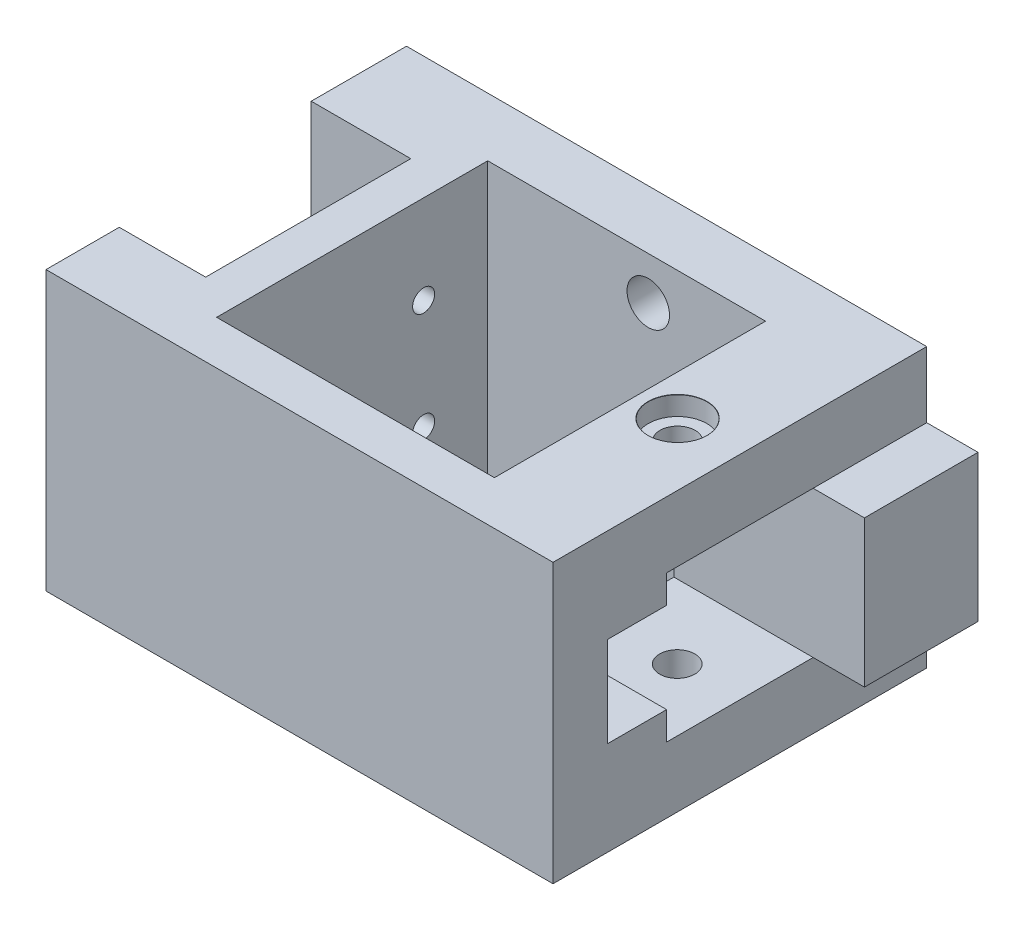
SolidWorks part; units mm, degrees
ref_plane "Alzado" through (0, 0, 0) normal (0, 0, 1) x (1, 0, 0)
ref_plane "Planta" through (0, 0, 0) normal (0, 1, 0) x (1, 0, 0)
ref_plane "Vista lateral" through (0, 0, 0) normal (1, 0, 0) x (0, 0, -1)
sketch "Croquis1" plane through (0, 0, 0) normal (0, 1, 0) x (1, 0, 0)
  line L0 (-121.6471, 30.8824) -> (-62.6471, 30.8824)
  line L1 (-62.6471, 30.8824) -> (-62.6471, -18.1176)
  line L2 (-62.6471, -18.1176) -> (-121.6471, -18.1176)
  line L3 (-121.6471, -7.1176) -> (-108.0588, -7.1176)
  line L4 (-108.0588, -7.1176) -> (-108.0588, 19.8824)
  line L5 (-108.0588, 19.8824) -> (-121.6471, 19.8824)
  line L6 (-121.6471, 19.8824) -> (-121.6471, 30.8824)
  line L7 (-121.6471, -7.1176) -> (-121.6471, -18.1176)
  dimension "D1" = 11
  dimension "D2" = 11
  dimension "D3" = 27
  dimension "D4" = 49
  dimension "D5" = 59
extrude "Saliente-Extruir1" add sketch "Croquis1" along normal blind 38
sketch "Croquis2" plane through (0, 38, 0) normal (0, 1, 0) x (1, 0, 0)
  line L0 (-108.0588, 19.8824) -> (-108.0588, 30.8824) construction
  line L1 (-62.6471, 30.8824) -> (-121.6471, 30.8824) construction
  line L2 (-108.0588, 19.8824) -> (-108.0588, -18.1176) construction
  line L3 (-121.6471, -18.1176) -> (-62.6471, -18.1176) construction
  line L4 (-102.5588, 24.8824) -> (-102.5588, -12.1176)
  line L5 (-102.5588, -12.1176) -> (-69.6471, -12.1176)
  line L6 (-69.6471, -12.1176) -> (-69.6471, 24.8824)
  line L7 (-69.6471, 24.8824) -> (-102.5588, 24.8824)
  line L8 (-62.6471, -18.1176) -> (-62.6471, 30.8824) construction
  dimension "D1" = 7
  dimension "D2" = 11
  dimension "D3" = 6
  dimension "D4" = 6
extrude "Cortar-Extruir1" cut sketch "Croquis2" against normal blind 38
sketch "Croquis3" plane through (-102.5588, 0, 0) normal (1, 0, 0) x (0, 0, -1)
  line L0 (19.4824, 32.1) -> (-6.7176, 32.1) construction
  line L1 (-6.7176, 32.1) -> (-6.7176, 5.9) construction
  line L2 (-6.7176, 5.9) -> (19.4824, 5.9) construction
  line L3 (19.4824, 5.9) -> (19.4824, 32.1) construction
  line L4 (-7.1176, 38) -> (-7.1176, 0) construction
  line L5 (19.8824, 0) -> (-7.1176, 0) construction
  circle A0 centre (16.1324, 10.875) radius 1.5
  circle A1 centre (16.1324, 25.875) radius 1.5
  circle A2 centre (-3.8676, 10.875) radius 1.5
  circle A3 centre (-3.8676, 25.875) radius 1.5
  dimension "D5" = 3
  dimension "D6" = 3
  dimension "D7" = 3.35
  dimension "D8" = 9.95
  dimension "D9" = 3.35
  dimension "D10" = 3
  dimension "D11" = 15
  dimension "D12" = 3
  dimension "D13" = 3
  dimension "D14" = 9.95
  dimension "D15" = 15
  dimension "D16" = 20
  dimension "D17" = 20
  dimension "D1" = 26.2
  dimension "D2" = 0.4
  dimension "D3" = 26.2
  dimension "D4" = 5.9
extrude "Cortar-Extruir3" cut sketch "Croquis3" against normal blind 10
sketch "Croquis5" plane through (0, 0, 7.1176) normal (0, 0, -1) x (-1, 0, 0)
  line L1 (121.6471, 0) -> (108.0588, 0)
  line L2 (121.6471, 0) -> (121.6471, 38)
  line L3 (121.6471, 38) -> (108.0588, 38)
  line L4 (108.0588, 0) -> (108.0588, 38)
extrude "Cortar-Extruir4" cut sketch "Croquis5" against normal blind 1
sketch "Croquis8" plane through (-62.6471, 0, 0) normal (1, 0, 0) x (0, 0, -1)
  line L0 (30.8824, 38) -> (30.8824, 0) construction
  line L1 (17.3824, 29) -> (-2.6176, 29)
  line L2 (17.3824, 29) -> (17.3824, 9)
  line L3 (17.3824, 9) -> (-2.6176, 9)
  line L4 (-2.6176, 29) -> (-2.6176, 9)
  line L5 (-18.1176, 38) -> (30.8824, 38) construction
  dimension "D1" = 20
  dimension "D2" = 20
  dimension "D3" = 20
  dimension "D4" = 13.5
  dimension "D5" = 9
extrude "Cortar-Extruir5" cut sketch "Croquis8" against normal blind 8
sketch "Croquis10" plane through (-62.6471, 0, 0) normal (1, 0, 0) x (0, 0, -1)
  line L0 (-2.6176, 25) -> (-10.6176, 25)
  line L1 (-10.6176, 13) -> (-2.6176, 13)
  line L2 (-2.6176, 29) -> (-2.6176, 9) construction
  line L3 (-2.6176, 13) -> (-2.6176, 25)
  line L4 (-10.6176, 25) -> (-10.6176, 13)
  line L5 (17.3824, 29) -> (-2.6176, 29) construction
  dimension "D1" = 12
  dimension "D2" = 8
  dimension "D3" = 4
extrude "Cortar-Extruir7" cut sketch "Croquis10" against normal blind 10
sketch "Croquis11" plane through (-121.6471, 0, 0) normal (-1, 0, 0) x (0, 0, 1)
  line L1 (8.1176, 38) -> (18.1176, 38)
  line L2 (8.1176, 38) -> (8.1176, 0)
  line L3 (8.1176, 0) -> (18.1176, 0)
  line L4 (18.1176, 38) -> (18.1176, 0)
extrude "Cortar-Extruir8" cut sketch "Croquis11" against normal blind 1.8
sketch "Croquis12" plane through (-62.6471, 0, 0) normal (1, 0, 0) x (0, 0, -1)
  line L1 (17.3824, 9) -> (22.3824, 9)
  line L2 (17.3824, 9) -> (17.3824, 29)
  line L3 (17.3824, 29) -> (22.3824, 29)
  line L4 (22.3824, 9) -> (22.3824, 29)
  dimension "D1" = 5
sketch "Croquis13" plane through (-62.6471, 0, 0) normal (1, 0, 0) x (0, 0, -1)
  line L0 (30.8824, 0) -> (30.8824, 38)
  line L1 (30.8824, 38) -> (-18.1176, 38)
  line L2 (-18.1176, 38) -> (-18.1176, 0)
  line L3 (-18.1176, 0) -> (30.8824, 0)
  line L4 (17.3824, 9) -> (17.3824, 29)
  line L5 (17.3824, 29) -> (-2.6176, 29)
  line L6 (-2.6176, 29) -> (-2.6176, 25)
  line L7 (-2.6176, 25) -> (-10.6176, 25)
  line L8 (-10.6176, 25) -> (-10.6176, 13)
  line L9 (-10.6176, 13) -> (-2.6176, 13)
  line L10 (-2.6176, 13) -> (-2.6176, 9)
  line L11 (-2.6176, 9) -> (17.3824, 9)
extrude "Saliente-Extruir2" add sketch "Croquis13" along normal blind 12
sketch "Croquis15" plane through (0, 0, -30.8824) normal (0, 0, -1) x (-1, 0, 0)
  line L1 (121.6471, 0) -> (50.6471, 0)
  line L2 (121.6471, 0) -> (121.6471, 38)
  line L3 (121.6471, 38) -> (50.6471, 38)
  line L4 (50.6471, 0) -> (50.6471, 38)
extrude "Saliente-Extruir3" add sketch "Croquis15" along normal blind 2
hole_wizard "Refrentado para tornillo con cabeza plana de M51" positions "Croquis16" profile "Croquis17" counterbore size "M5" standard "DIN"
sketch "Croquis16" plane through (0, 0, -32.8824) normal (0, 0, -1) x (-1, 0, 0)
  line L0 (50.6471, 0) -> (121.6471, 0) construction
  line L1 (121.6471, 38) -> (50.6471, 38) construction
  line L2 (50.6471, 38) -> (50.6471, 0) construction
  line L3 (50.6471, 38) -> (50.6471, 0) construction
  point P0 (81.6471, 5.85)
  point P2 (80.6471, 32.15)
  dimension "D1" = 5.85
  dimension "D2" = 5.85
  dimension "D3" = 30
  dimension "D4" = 31
sketch "Croquis17" plane through (-81.6471, 5.85, -32.8824) normal (1, 0, 0) x (0, 1, 0)
  line L0 (0, 0) -> (0, 21.7425)
  line L1 (0, 21.7425) -> (2.9, 20)
  line L2 (2.9, 20) -> (2.9, 3.3)
  line L3 (2.9, 3.3) -> (5, 3.3)
  line L5 (5, 3.3) -> (5, 0.2)
  line L6 (5, 0.2) -> (5.2, 0)
  line L7 (5.2, 0) -> (0, 0)
  line L8 (-5, 0.2) -> (-5.2, 0) construction
  line L10 (0, 21.7425) -> (-2.9, 20) construction
  line L11 (0, -6.35) -> (0, 107.95) construction
  dimension "Diámetro de taladro" = 5.8
  dimension "Profundidad de taladro" = 20
  dimension "Diámetro de refrentado" = 10
  dimension "Profundidad de refrentado" = 3.3
  dimension "Diámetro de avellanado cercano" = 10.4
  dimension "Ángulo de avellanado cercano" = 90
  dimension "Ángulo de perforador" = 118
sketch "Croquis18" plane through (0, 13, 0) normal (0, 1, 0) x (1, 0, 0)
  line L0 (-50.6471, -10.6176) -> (-50.6471, -2.6176) construction
  line L1 (-50.6471, -10.6176) -> (-69.6471, -10.6176)
  line L2 (-50.6471, -10.6176) -> (-50.6471, -2.6176)
  line L3 (-50.6471, -2.6176) -> (-69.6471, -2.6176)
  line L4 (-69.6471, -10.6176) -> (-69.6471, -2.6176)
extrude "Cortar-Extruir9" cut sketch "Croquis18" against normal blind 0.16
sketch "Croquis19" plane through (0, 25, 0) normal (0, -1, 0) x (-1, 0, 0)
  line L1 (69.6471, -10.6176) -> (50.6471, -10.6176)
  line L2 (69.6471, -10.6176) -> (69.6471, -2.6176)
  line L3 (69.6471, -2.6176) -> (50.6471, -2.6176)
  line L4 (50.6471, -10.6176) -> (50.6471, -2.6176)
extrude "Cortar-Extruir10" cut sketch "Croquis19" against normal blind 0.16
sketch "Croquis20" plane through (0, 0, 10.6176) normal (0, 0, -1) x (-1, 0, 0)
  line L1 (50.6471, 12.84) -> (69.6471, 12.84)
  line L2 (50.6471, 12.84) -> (50.6471, 25.16)
  line L3 (50.6471, 25.16) -> (69.6471, 25.16)
  line L4 (69.6471, 12.84) -> (69.6471, 25.16)
extrude "Cortar-Extruir11" cut sketch "Croquis20" against normal blind 0.1
sketch "Croquis21" plane through (0, 0, 0) normal (0, -1, 0) x (-1, 0, 0)
  line L0 (50.6471, 16.3824) -> (69.6471, 16.3824) construction
  line L1 (50.6471, -18.1176) -> (50.6471, 32.8824) construction
  line L2 (69.6471, -12.1176) -> (69.6471, 24.8824) construction
  line L3 (50.6471, 32.8824) -> (121.6471, 32.8824) construction
  line L4 (50.6471, -2.6176) -> (69.6471, -2.6176) construction
  line L5 (119.8471, -18.1176) -> (50.6471, -18.1176) construction
  point P12 (60.1471, -2.6176)
  dimension "D1" = 16.5
  dimension "D2" = 15.5
hole_wizard "Refrentado para tornillo con cabeza plana de M41" positions "Croquis22" profile "Croquis23" counterbore size "M4" standard "DIN"
sketch "Croquis22" plane through (0, 0, 0) normal (0, -1, 0) x (-1, 0, 0)
  line L0 (50.6471, -2.6176) -> (69.6471, -2.6176) construction
  line L1 (50.6471, -18.1176) -> (50.6471, 32.8824) construction
  point P0 (59.1471, 7.3322)
  point P5 (60.1471, -2.6176)
  dimension "D1" = 10
  dimension "D2" = 8.5
sketch "Croquis23" plane through (-59.1471, 0, -7.3322) normal (1, 0, 0) x (0, 0, -1)
  line L0 (0, 0) -> (0, 21.4421)
  line L1 (0, 21.4421) -> (2.4, 20)
  line L2 (2.4, 20) -> (2.4, 2.6)
  line L3 (2.4, 2.6) -> (4, 2.6)
  line L5 (4, 2.6) -> (4, 0.025)
  line L6 (4, 0.025) -> (4.025, 0)
  line L7 (4.025, 0) -> (0, 0)
  line L8 (-4, 0.025) -> (-4.025, 0) construction
  line L10 (0, 21.4421) -> (-2.4, 20) construction
  line L11 (0, -6.35) -> (0, 107.95) construction
  dimension "Diámetro de taladro" = 4.8
  dimension "Profundidad de taladro" = 20
  dimension "Diámetro de refrentado" = 8
  dimension "Profundidad de refrentado" = 2.6
  dimension "Diámetro de avellanado cercano" = 8.05
  dimension "Ángulo de avellanado cercano" = 90
  dimension "Ángulo de perforador" = 118
hole_wizard "Refrentado para tornillo con cabeza plana de M42" positions "Croquis24" profile "Croquis25" counterbore size "M4" standard "DIN"
sketch "Croquis24" plane through (0, 38, 0) normal (0, 1, 0) x (1, 0, 0)
  line L0 (-119.8471, -18.1176) -> (-50.6471, -18.1176) construction
  line L1 (-50.6471, 32.8824) -> (-50.6471, -18.1176) construction
  point P0 (-59.1471, 7.3824)
  dimension "D1" = 25.5
  dimension "D2" = 8.5
sketch "Croquis25" plane through (-59.1471, 38, -7.3824) normal (1, 0, 0) x (0, 0, 1)
  line L0 (0, 0) -> (0, 21.4421)
  line L1 (0, 21.4421) -> (2.4, 20)
  line L2 (2.4, 20) -> (2.4, 2.6)
  line L3 (2.4, 2.6) -> (4, 2.6)
  line L5 (4, 2.6) -> (4, 0.025)
  line L6 (4, 0.025) -> (4.025, 0)
  line L7 (4.025, 0) -> (0, 0)
  line L8 (-4, 0.025) -> (-4.025, 0) construction
  line L10 (0, 21.4421) -> (-2.4, 20) construction
  line L11 (0, -6.35) -> (0, 107.95) construction
  dimension "Diámetro de taladro" = 4.8
  dimension "Profundidad de taladro" = 20
  dimension "Diámetro de refrentado" = 8
  dimension "Profundidad de refrentado" = 2.6
  dimension "Diámetro de avellanado cercano" = 8.05
  dimension "Ángulo de avellanado cercano" = 90
  dimension "Ángulo de perforador" = 118
chamfer "Chaflán3" distance 5 angle 45 2 edges at (-69.6471, 0, -6.3824) (-69.6471, 38, -6.3824)
sketch "Croquis26" plane through (-50.6471, 0, 0) normal (1, 0, 0) x (0, 0, -1)
  line L0 (32.8824, 38) -> (32.8824, 0) construction
  line L1 (17.3824, 9) -> (32.8824, 9)
  line L2 (17.3824, 9) -> (17.3824, 29)
  line L3 (17.3824, 29) -> (32.8824, 29)
  line L4 (32.8824, 9) -> (32.8824, 29)
extrude "Saliente-Extruir4" add sketch "Croquis26" along normal blind 7
